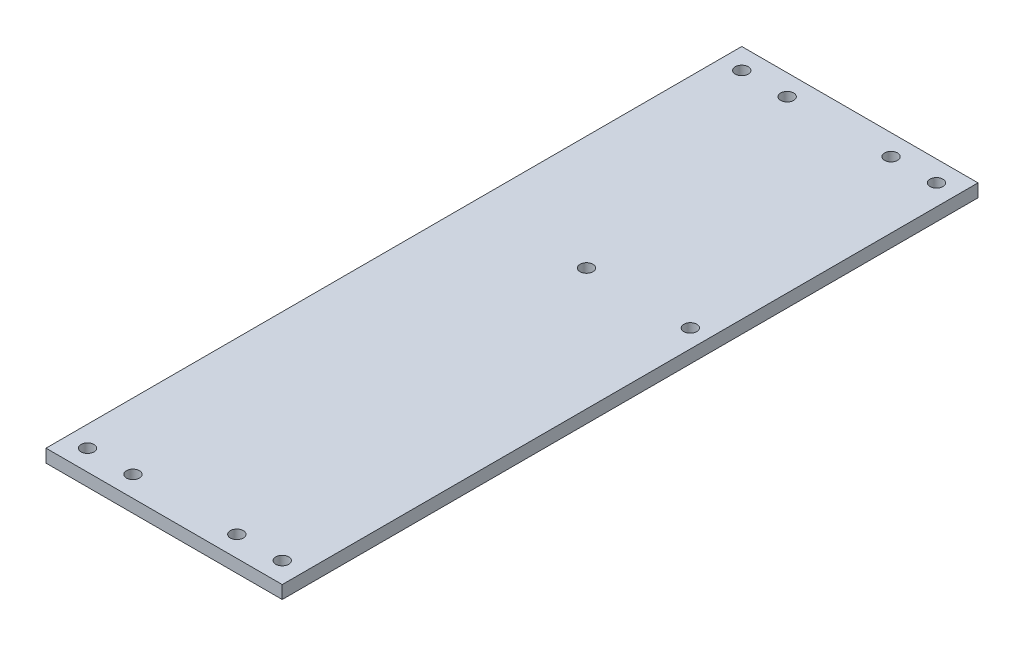
SolidWorks part; units mm, degrees
ref_plane "Ebene vorne" through (0, 0, 0) normal (0, 0, 1) x (1, 0, 0)
ref_plane "Ebene oben" through (0, 0, 0) normal (0, 1, 0) x (1, 0, 0)
ref_plane "Ebene rechts" through (0, 0, 0) normal (1, 0, 0) x (0, 0, -1)
sketch "Skizze1" plane through (0, 0, 0) normal (0, 1, 0) x (1, 0, 0)
  line L2 (-36.25, -134) -> (36.25, -134)
  line L3 (-36.25, -134) -> (-36.25, 134)
  line L4 (-36.25, 134) -> (36.25, 134)
  line L5 (36.25, -134) -> (36.25, 134)
  line L6 (-36.25, -134) -> (36.25, 134) construction
  line L7 (-36.25, 134) -> (36.25, -134) construction
  point P1 (0, 0)
  dimension "D1" = 72.5
  dimension "D2" = 268
extrude "Aufsatz-Linear austragen1" add sketch "Skizze1" along normal blind 5
hole_wizard "M6 Gewindebohrung2" positions "Skizze4" profile "Skizze3" tap size "M6" standard "DIN" end condition up to next
sketch "Skizze4" plane through (0, 5, 0) normal (0, 1, 0) x (1, 0, 0)
  line L0 (-36.25, 134) -> (-36.25, -134) construction
  line L1 (-36.25, -134) -> (36.25, -134) construction
  line L2 (-29.25, -126) -> (10.75, -126) construction
  line L3 (10.75, -126) -> (10.75, 126) construction
  line L4 (10.75, 126) -> (-29.25, 126) construction
  line L5 (-29.25, 126) -> (-29.25, -126) construction
  point P0 (-29.25, -126)
  point P2 (10.75, -126)
  point P4 (-29.25, 126)
  point P6 (10.75, 126)
  dimension "D1" = 7
  dimension "D2" = 8
  dimension "D3" = 40
  dimension "D4" = 252
sketch "Skizze3" plane through (-29.25, 5, 126) normal (1, 0, 0) x (0, 0, 1)
  line L0 (0, 0) -> (0, 5)
  line L1 (0, 5) -> (2.5, 5)
  line L2 (2.5, 5) -> (2.5, 0)
  line L5 (2.5, 0) -> (0, 0)
  line L11 (0, -6.35) -> (0, 107.95) construction
  dimension "Bohrerdurchmesser" = 5
  dimension "Bohrungstiefe" = 5
cosmetic thread "Bohrungsgewinde1" parameters "D2"=6
cosmetic thread "Bohrungsgewinde2" parameters "D2"=6
cosmetic thread "Bohrungsgewinde3" parameters "D2"=6
cosmetic thread "Bohrungsgewinde4" parameters "D2"=6
hole_wizard "M6 Gewindebohrung1" positions "Skizze5" profile "Skizze6" tap size "M6" standard "DIN" end condition up to next
sketch "Skizze5" plane through (0, 5, 0) normal (0, 1, 0) x (1, 0, 0)
  line L0 (-36.25, 30.2) -> (36.25, 30.2) construction
  line L1 (-36.25, 134) -> (-36.25, -134) construction
  line L2 (36.25, -134) -> (36.25, 134) construction
  line L3 (-36.25, -134) -> (36.25, -134) construction
  point P9 (-10.75, 30.2)
  point P11 (29.25, 30.2)
  dimension "D1" = 25.5
  dimension "D2" = 40
  dimension "D3" = 164.2
sketch "Skizze6" plane through (29.25, 5, -30.2) normal (1, 0, 0) x (0, 0, 1)
  line L0 (0, 0) -> (0, 5)
  line L1 (0, 5) -> (2.5, 5)
  line L2 (2.5, 5) -> (2.5, 0)
  line L5 (2.5, 0) -> (0, 0)
  line L11 (0, -6.35) -> (0, 107.95) construction
  dimension "Bohrerdurchmesser" = 5
  dimension "Bohrungstiefe" = 5
cosmetic thread "Bohrungsgewinde5" parameters "D2"=6
cosmetic thread "Bohrungsgewinde6" parameters "D2"=6
sketch "Skizze7" plane through (-36.25, 0, 0) normal (-1, 0, 0) x (0, 0, 1)
  line L4 (-134, 0) -> (134, 0)
  line L5 (134, 0) -> (134, 5)
  line L6 (134, 5) -> (-134, 5)
  line L7 (-134, 5) -> (-134, 0)
  line L8 (-134, 0) -> (134, 0)
  line L9 (134, 0) -> (134, 5)
  line L10 (134, 5) -> (-134, 5)
  line L11 (-134, 5) -> (-134, 0)
  dimension "D1" = 0
extrude "Aufsatz-Linear austragen2" add sketch "Skizze7" along normal blind 18.5
hole_wizard "M6 Gewindebohrung3" positions "Skizze9" profile "Skizze10" tap size "M6" standard "DIN" end condition up to next
sketch "Skizze9" plane through (0, 5, 0) normal (0, 1, 0) x (1, 0, 0)
  line L0 (-9.25, -134) -> (-9.25, 134) construction
  line L1 (-54.75, -134) -> (36.25, -134) construction
  line L2 (36.25, 134) -> (-54.75, 134) construction
  line L5 (-54.75, 0) -> (36.25, 0) construction
  line L6 (-54.75, -134) -> (-54.75, 134) construction
  line L7 (36.25, -134) -> (36.25, 134) construction
  point P0 (-46.75, -126)
  point P19 (28.25, -126)
  point P20 (28.25, 126)
  point P21 (-46.75, 126)
  dimension "D1" = 8
  dimension "D2" = 8
sketch "Skizze10" plane through (-46.75, 5, 126) normal (1, 0, 0) x (0, 0, 1)
  line L0 (0, 0) -> (0, 5)
  line L1 (0, 5) -> (2.5, 5)
  line L2 (2.5, 5) -> (2.5, 0)
  line L5 (2.5, 0) -> (0, 0)
  line L11 (0, -6.35) -> (0, 107.95) construction
  dimension "Bohrerdurchmesser" = 5
  dimension "Bohrungstiefe" = 5
cosmetic thread "Bohrungsgewinde7" parameters "D2"=6
cosmetic thread "Bohrungsgewinde8" parameters "D2"=6
cosmetic thread "Bohrungsgewinde9" parameters "D2"=6
cosmetic thread "Bohrungsgewinde10" parameters "D2"=6
